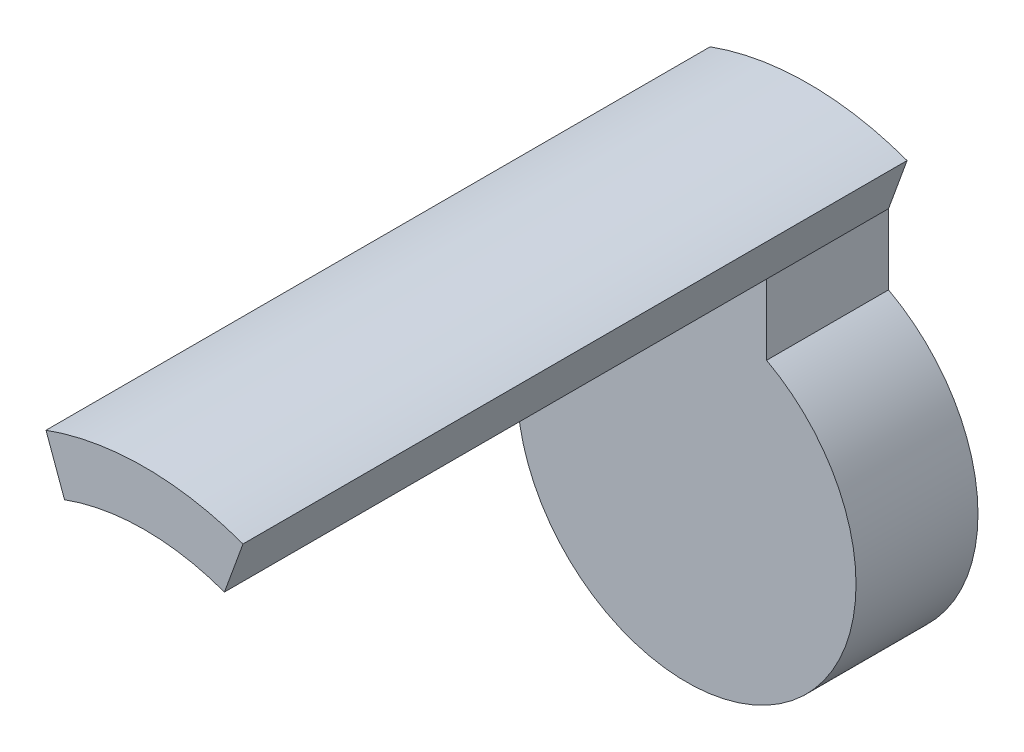
SolidWorks part; units mm, degrees
ref_plane "정면" through (0, 0, 0) normal (0, 0, 1) x (1, 0, 0)
ref_plane "윗면" through (0, 0, 0) normal (0, 1, 0) x (1, 0, 0)
ref_plane "우측면" through (0, 0, 0) normal (1, 0, 0) x (0, 0, -1)
sketch "스케치1" plane through (0, 0, 0) normal (0, 0, 1) x (1, 0, 0)
  circle A0 centre (0, 0) radius 3.6
  circle A1 centre (0, 0) radius 8.5
  circle A2 centre (6.125, 0) radius 1.25
  circle A3 centre (-6.8, 0) radius 0.6
  dimension "D1" = 7.2
  dimension "D2" = 17
  dimension "D3" = 2.5
  dimension "D5" = 1.2
  dimension "D4" = 6.125
  dimension "D6" = 6.8
extrude "보스-돌출1" add sketch "스케치1" along normal blind 9
sketch "스케치2" plane through (0, 0, 9) normal (0, 0, 1) x (1, 0, 0)
  circle A0 centre (0, 0) radius 4.3
  dimension "D1" = 8.6
extrude "컷-돌출1" cut sketch "스케치2" against normal blind 0.8
sketch "스케치3" plane through (0, 0, 0) normal (0, 0, -1) x (-1, 0, 0)
  circle A0 centre (0, 0) radius 5.9
  circle A1 centre (0, 0) radius 3.6
  dimension "D1" = 11.8
extrude "보스-돌출2" add sketch "스케치3" along normal blind 2.5
sketch "스케치4" plane through (0, 0, 0) normal (1, 0, 0) x (0, 0, -1)
  line L0 (1.25, 5.9) -> (1.25, -5.9) construction
  line L1 (2.5, 5.9) -> (0, 5.9) construction
  line L2 (0, -5.9) -> (2.5, -5.9) construction
  line L3 (2.5, 5.9) -> (0, 5.9)
  line L4 (2.5, -5.9) -> (2.5, 5.9) construction
  line L5 (0, -8.5) -> (0, 8.5) construction
  line L6 (0, -5.9) -> (0, 5.9) construction
  line L7 (0, 5.9) -> (1.25, 4.6)
  line L8 (1.25, 4.6) -> (2.5, 5.9)
  line L9 (0, 0) -> (2.5, 0) construction
  dimension "D1" = 1.3
  dimension "D2" = 2.5
  dimension "D3" = 4.6
revolve "컷-회전1" cut sketch "스케치4" angle 360 about L9
sketch "스케치5" plane through (0, 0, -2.5) normal (0, 0, -1) x (-1, 0, 0)
  circle A0 centre (0, 0) radius 4.3
  dimension "D1" = 8.6
extrude "컷-돌출2" cut sketch "스케치5" against normal blind 0.8
sketch "스케치6" plane through (0, 0, 0) normal (0, 0, -1) x (-1, 0, 0)
  line L0 (0, 0) -> (-2.9072, 7.9874) construction
  line L1 (0, 0) -> (0, 8.5) construction
  line L2 (-2.9072, 7.9874) -> (-2.3599, 6.4839)
  line L3 (2.9072, 7.9874) -> (2.3599, 6.4839)
  arc A0 (-2.9072, 7.9874) -> (2.9072, 7.9874) centre (0, 0) cw
  circle A1 centre (0, 0) radius 8.5 construction
  arc A2 (-2.3599, 6.4839) -> (2.3599, 6.4839) centre (0, 0) cw
  dimension "D1" = 1.6
  dimension "D2" = 20
extrude "보스-돌출3" add sketch "스케치6" along normal blind 7
sketch "스케치10" plane through (0, 0, -7) normal (0, 0, -1) x (-1, 0, 0)
  line L0 (2.3599, 6.4839) -> (2.9072, 7.9874) construction
  line L1 (2.3599, 6.4839) -> (2.9072, 7.9874)
  arc A0 (-2.9072, 7.9874) -> (2.9072, 7.9874) centre (0, 0) ccw construction
  arc A1 (2.3599, 6.4839) -> (-2.3599, 6.4839) centre (0, 0) ccw construction
  arc A2 (-2.9072, 7.9874) -> (2.9072, 7.9874) centre (0, 0) ccw
  arc A3 (2.3599, 6.4839) -> (-2.3599, 6.4839) centre (0, 0) ccw
  line M5 (-2.9072, 7.9874) -> (-2.3599, 6.4839)
  arc M6 (-2.3599, 6.4839) -> (2.3599, 6.4839) centre (0, 0) cw
  line M7 (2.3599, 6.4839) -> (2.9072, 7.9874)
extrude "컷-돌출6" cut sketch "스케치10" against normal through all and the other way through all contours A2 M5 M7 M6
sketch "스케치9" plane through (0, 0, -7) normal (0, 0, -1) x (-1, 0, 0)
  line L4 (-3.4168, 8.218) -> (-2.5948, 5.9596)
  line L5 (2.5948, 5.9596) -> (3.4168, 8.218)
  line L6 (-3.4168, 8.218) -> (-2.5948, 5.9596)
  line L7 (2.5948, 5.9596) -> (3.4168, 8.218)
  arc A4 (3.4168, 8.218) -> (-3.4168, 8.218) centre (0, 0) ccw
  arc A5 (2.5948, 5.9596) -> (-2.5948, 5.9596) centre (0, 0) ccw
  arc A6 (3.4168, 8.218) -> (-3.4168, 8.218) centre (0, 0) ccw
  arc A7 (2.5948, 5.9596) -> (-2.5948, 5.9596) centre (0, 0) ccw
  dimension "D1" = 0.4
extrude "컷-돌출4" [suppressed] cut sketch "스케치9" against normal through all
sketch "스케치7" plane through (0, 0, -7) normal (0, 0, -1) x (-1, 0, 0)
  line L0 (-2.3599, 6.4839) -> (-2.3599, 4.408)
  line L1 (2.3599, 6.4839) -> (2.3599, 4.408)
  line L2 (-2.9072, 7.9874) -> (-2.3599, 6.4839)
  line L3 (2.3599, 6.4839) -> (2.9072, 7.9874)
  line L4 (-2.9072, 7.9874) -> (-2.3599, 6.4839)
  line L5 (2.3599, 6.4839) -> (2.9072, 7.9874)
  arc A1 (-2.3599, 4.408) -> (2.3599, 4.408) centre (0, 0) ccw
  arc A4 (2.9072, 7.9874) -> (-2.9072, 7.9874) centre (0, 0) ccw
  arc A5 (2.3599, 6.4839) -> (-2.3599, 6.4839) centre (0, 0) ccw
  arc A6 (2.9072, 7.9874) -> (-2.9072, 7.9874) centre (0, 0) ccw
  point P2 (2.3599, 3.0947)
  point P11 (0, 0)
  point P13 (0, 0)
  dimension "D3" = 10
  dimension "D1" = 0
extrude "보스-돌출4" add sketch "스케치7" along normal blind 3.6
sketch "스케치8" plane through (0, 0, -10.6) normal (0, 0, -1) x (-1, 0, 0)
  circle A0 centre (0, 0) radius 3.2
  dimension "D1" = 6.4
extrude "컷-돌출3" cut sketch "스케치8" against normal blind 2
